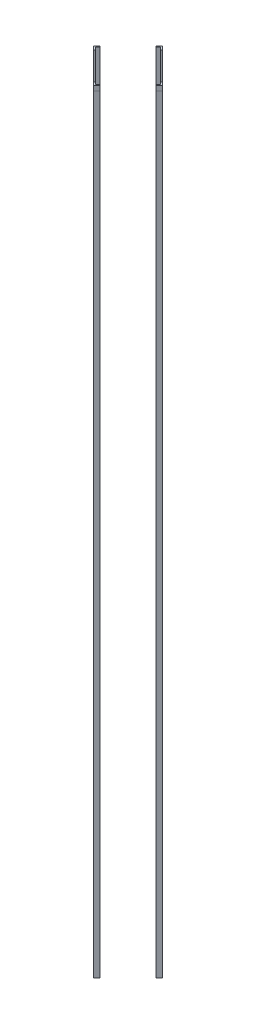
SolidWorks part; units mm, degrees
ref_plane "Front Plane" through (0, 0, 0) normal (0, 0, 1) x (1, 0, 0)
ref_plane "Top Plane" through (0, 0, 0) normal (0, 1, 0) x (1, 0, 0)
ref_plane "Right Plane" through (0, 0, 0) normal (1, 0, 0) x (0, 0, -1)
sketch "Sketch2" plane through (0, 0, 0) normal (0, 1, 0) x (1, 0, 0)
  line L0 (0, 94.7743) -> (-8.9803, 85.794)
  line L1 (-8.9803, 85.794) -> (-6.7352, 83.549)
  line L2 (-6.7352, 83.549) -> (0, 90.2842)
  line L3 (0, 90.2842) -> (6.7352, 83.549)
  line L4 (6.7352, 83.549) -> (8.9803, 85.794)
  line L5 (8.9803, 85.794) -> (0, 94.7743)
  line L6 (0, 0) -> (0, 186.644) construction
  line L7 (94.7743, 0) -> (85.794, 8.9803)
  line L8 (85.794, 8.9803) -> (83.549, 6.7352)
  line L9 (83.549, 6.7352) -> (90.2842, 0)
  line L10 (90.2842, 0) -> (83.549, -6.7352)
  line L11 (83.549, -6.7352) -> (85.794, -8.9803)
  line L12 (85.794, -8.9803) -> (94.7743, 0)
  line L13 (0, -94.7743) -> (8.9803, -85.794)
  line L14 (8.9803, -85.794) -> (6.7352, -83.549)
  line L15 (6.7352, -83.549) -> (0, -90.2842)
  line L16 (0, -90.2842) -> (-6.7352, -83.549)
  line L17 (-6.7352, -83.549) -> (-8.9803, -85.794)
  line L18 (-8.9803, -85.794) -> (0, -94.7743)
  line L19 (-94.7743, 0) -> (-85.794, -8.9803)
  line L20 (-85.794, -8.9803) -> (-83.549, -6.7352)
  line L21 (-83.549, -6.7352) -> (-90.2842, 0)
  line L22 (-90.2842, 0) -> (-83.549, 6.7352)
  line L23 (-83.549, 6.7352) -> (-85.794, 8.9803)
  line L24 (-85.794, 8.9803) -> (-94.7743, 0)
  point P31 (0, 0)
  dimension "D2" = 12.7
  dimension "D3" = 12.7
  dimension "D4" = 3.175
  dimension "D5" = 3.175
  dimension "D6" = 4
extrude "Boss-Extrude1" add sketch "Sketch2" along normal blind 2133.6
sketch "Sketch3" plane through (47.3871, 0, 47.3871) normal (0.7071, 0, 0.7071) x (0.7071, 0, -0.7071)
  line L0 (-54.3155, 2133.6) -> (-54.3155, 0) construction
  line L1 (-67.0155, 2133.6) -> (-54.3155, 2133.6)
  line L2 (-67.0155, 2133.6) -> (-67.0155, 2120.9)
  line L3 (-67.0155, 2120.9) -> (-54.3155, 2120.9)
  line L4 (-54.3155, 2133.6) -> (-54.3155, 2120.9)
  dimension "D1" = 12.7
extrude "Boss-Extrude2" add sketch "Sketch3" along normal blind 0.0254
sketch "Sketch4" plane through (47.3871, 0, 47.3871) normal (0.7071, 0, 0.7071) x (0.7071, 0, -0.7071)
  line L0 (67.0155, 2133.6) -> (67.0155, 0) construction
  line L1 (54.3155, 2133.6) -> (67.0155, 2133.6)
  line L2 (54.3155, 2133.6) -> (54.3155, 2120.9)
  line L3 (54.3155, 2120.9) -> (67.0155, 2120.9)
  line L4 (67.0155, 2133.6) -> (67.0155, 2120.9)
  dimension "D1" = 12.7
extrude "Boss-Extrude3" add sketch "Sketch4" along normal blind 0.0254
